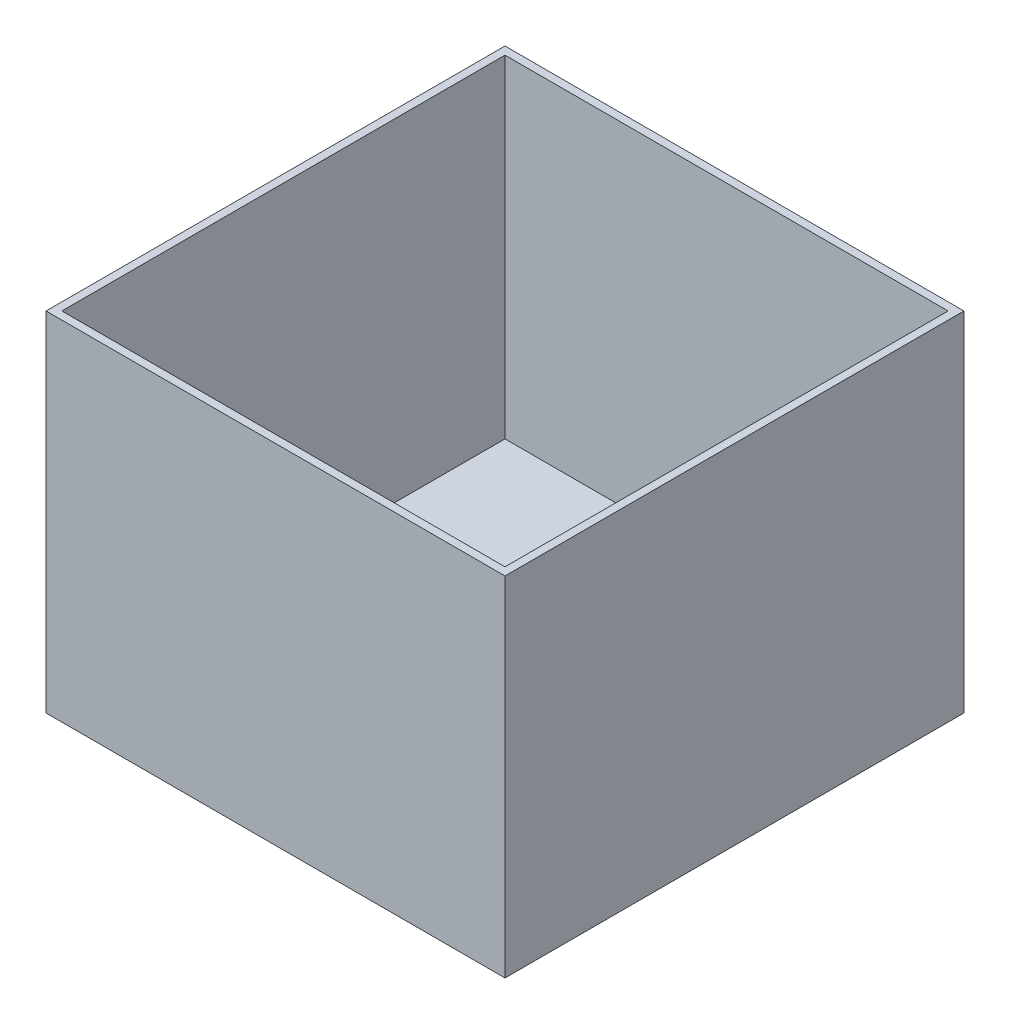
SolidWorks part; units mm, degrees
ref_plane "Front" through (0, 0, 0) normal (0, 0, 1) x (1, 0, 0)
ref_plane "Top" through (0, 0, 0) normal (0, 1, 0) x (1, 0, 0)
ref_plane "Right" through (0, 0, 0) normal (1, 0, 0) x (0, 0, -1)
sketch "Sketch1" plane through (0, 0, 0) normal (0, 1, 0) x (1, 0, 0)
  line L1 (-92.075, -92.075) -> (92.075, -92.075)
  line L2 (-92.075, -92.075) -> (-92.075, 92.075)
  line L3 (-92.075, 92.075) -> (92.075, 92.075)
  line L4 (92.075, -92.075) -> (92.075, 92.075)
  line L5 (-92.075, -92.075) -> (92.075, 92.075) construction
  line L6 (-92.075, 92.075) -> (92.075, -92.075) construction
  point P0 (0, 0)
  dimension "D1" = 184.15
  dimension "D2" = 184.15
extrude "Boss-Extrude1" add sketch "Sketch1" along normal blind 139.7
sketch "Sketch2" plane through (0, 139.7, 0) normal (0, 1, 0) x (1, 0, 0)
  line L1 (-88.9, 88.9) -> (88.9, 88.9)
  line L2 (-88.9, 88.9) -> (-88.9, -88.9)
  line L3 (-88.9, -88.9) -> (88.9, -88.9)
  line L4 (88.9, 88.9) -> (88.9, -88.9)
  line L5 (-88.9, 88.9) -> (88.9, -88.9) construction
  line L6 (-88.9, -88.9) -> (88.9, 88.9) construction
  point P0 (0, 0)
  dimension "D1" = 177.8
  dimension "D2" = 177.8
extrude "Cut-Extrude1" cut sketch "Sketch2" against normal blind 133.35
sketch "Sketch3" plane through (0, 6.35, 0) normal (0, 1, 0) x (1, 0, 0)
  line L0 (-92.075, 92.075) -> (-92.075, -92.075) construction
  line L1 (92.075, 92.075) -> (-92.075, 92.075) construction
  circle A0 centre (-1.016, 78.6514) radius 5.842
  point P4 (0, 92.075)
  dimension "D2" = 13.462
  dimension "D1" = 91.059
extrude "Boss-Extrude2" add sketch "Sketch3" along normal blind 6.604
sketch "Sketch4" plane through (0, 6.35, 0) normal (0, 1, 0) x (1, 0, 0)
  line L0 (-92.075, 0) -> (92.075, 0) construction
  line L1 (-92.075, 92.075) -> (-92.075, -92.075) construction
  line L2 (92.075, -92.075) -> (92.075, 92.075) construction
